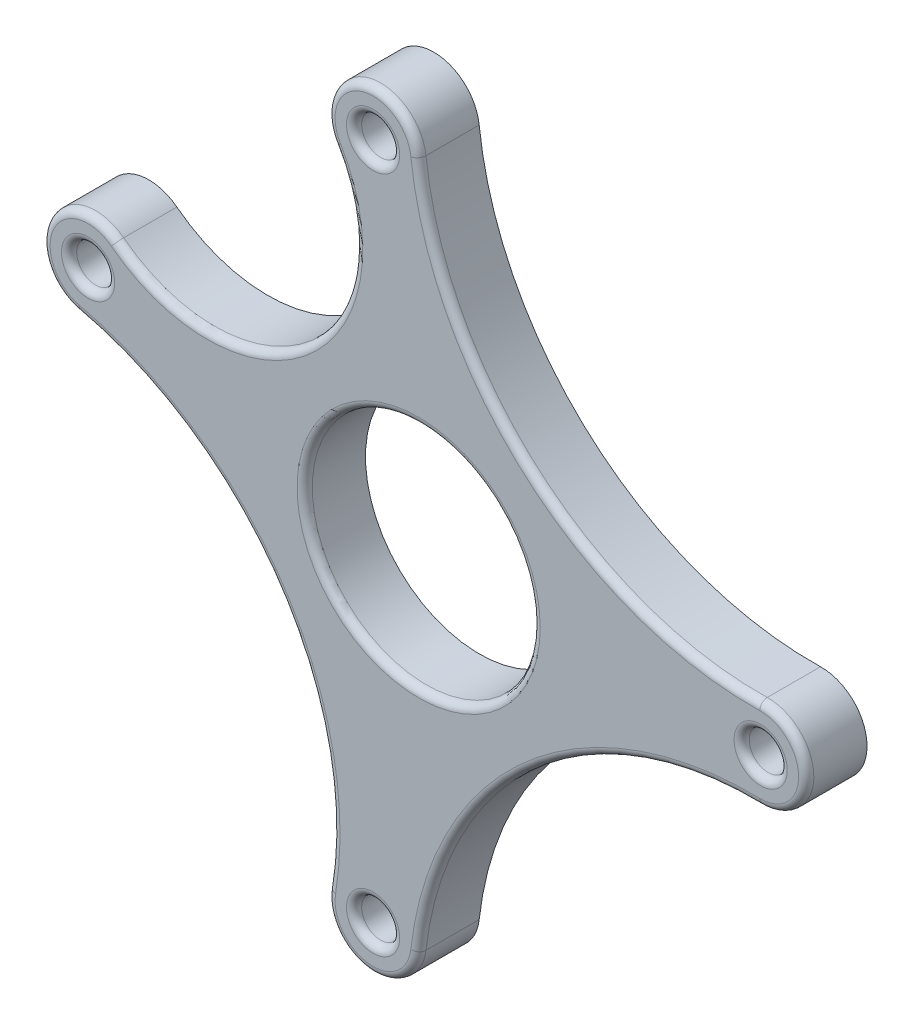
SolidWorks part; units mm, degrees
ref_plane "Plano frontal" through (0, 0, 0) normal (0, 0, 1) x (1, 0, 0)
ref_plane "Plano superior" through (0, 0, 0) normal (0, 1, 0) x (1, 0, 0)
ref_plane "Plano direito" through (0, 0, 0) normal (1, 0, 0) x (0, 0, -1)
sketch "Esboço1" plane through (0, 0, 0) normal (0, 0, 1) x (1, 0, 0)
  line L0 (45, 0) -> (0, 0) construction
  line L1 (0, 0) -> (-6, -44.6) construction
  line L2 (-43.5, 11.3) -> (0, 0) construction
  line L3 (-6, 44.6) -> (0, 0) construction
  circle A1 centre (0, 0) radius 15
  circle A2 centre (-6, 44.6) radius 2.5
  circle A3 centre (45, 0) radius 2.5
  circle A4 centre (-43.5, 11.3) radius 2.5
  circle A5 centre (-6, -44.6) radius 2.5
  arc A6 (-0.0383, 45.2769) -> (-11.1405, 41.5057) centre (-6, 44.6) ccw
  arc A7 (44.8762, -5.9987) -> (44.8762, 5.9987) centre (45, 0) ccw
  arc A8 (-39.8196, 16.0387) -> (-44.843, 5.4522) centre (-43.5, 11.3) ccw
  arc A9 (-11.9202, -43.6246) -> (-0.0383, -45.2769) centre (-6, -44.6) ccw
  arc A10 (-39.8196, 16.0387) -> (-11.1405, 41.5057) centre (-27.8538, 31.4452) ccw
  arc A11 (-0.0383, 45.2769) -> (44.8762, 5.9987) centre (43.9621, 50.2724) ccw
  arc A12 (44.8762, -5.9987) -> (-0.0383, -45.2769) centre (43.9621, -50.2724) ccw
  arc A13 (-44.843, 5.4522) -> (-11.9202, -43.6246) centre (-54.5025, -36.6092) cw
  point P4 (0, 0)
  point P5 (-43.5, 11.3)
  point P6 (45, 0)
  point P7 (-6, -44.6)
  point P8 (-6, 44.6)
  dimension "D2" = 30
  dimension "D3" = 5
  dimension "D4" = 5
  dimension "D5" = 5
  dimension "D6" = 5
  dimension "D7" = 12
  dimension "D8" = 12
  dimension "D9" = 12
  dimension "D10" = 12
extrude "Ressalto-extrusão1" add sketch "Esboço1" along normal blind 8 contours A11 A7 A12 A9 A13 A8 A10 A6 | A1 | A4 | A2 | A3 | A5
fillet "Filete1" radius 1 1 edges at (15, 0, 8)
fillet "Filete2" radius 1 12 edges at (-3.5, -44.6, 8) (-3.5, 44.6, 8) (14.8108, 16.9379, 8) (51, 0, 8) (14.8108, -16.9379, 8) (-6.8264, -50.5428, 8) (-18.6634, -12.5669, 8) (-48.9207, 13.8722, 8) (-14.9009, 16.8587, 8) (-7.9298, 50.2812, 8) (-41, 11.3, 8) (47.5, 0, 8)
